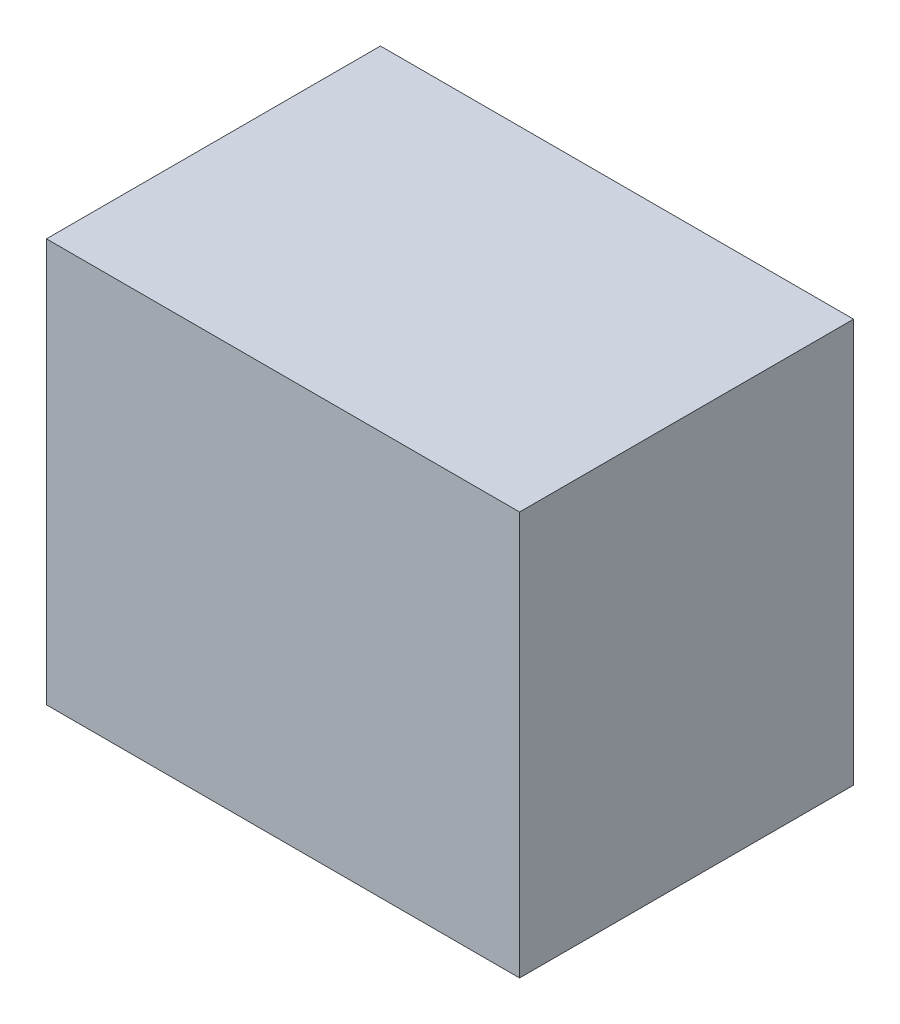
SolidWorks part; units mm, degrees
ref_plane "Płaszczyzna przednia" through (0, 0, 0) normal (0, 0, 1) x (1, 0, 0)
ref_plane "Płaszczyzna górna" through (0, 0, 0) normal (0, 1, 0) x (1, 0, 0)
ref_plane "Płaszczyzna prawa" through (0, 0, 0) normal (1, 0, 0) x (0, 0, -1)
sketch "Sketch1" plane through (0, 0, 0) normal (0, 1, 0) x (1, 0, 0)
  line L1 (-170, -120) -> (170, -120)
  line L2 (-170, -120) -> (-170, 120)
  line L3 (-170, 120) -> (170, 120)
  line L4 (170, -120) -> (170, 120)
  line L5 (-170, -120) -> (170, 120) construction
  line L6 (-170, 120) -> (170, -120) construction
  point P0 (0, 0)
  dimension "D1" = 340
  dimension "D2" = 240
extrude "Boss-Extrude1" add sketch "Sketch1" along normal blind 290
